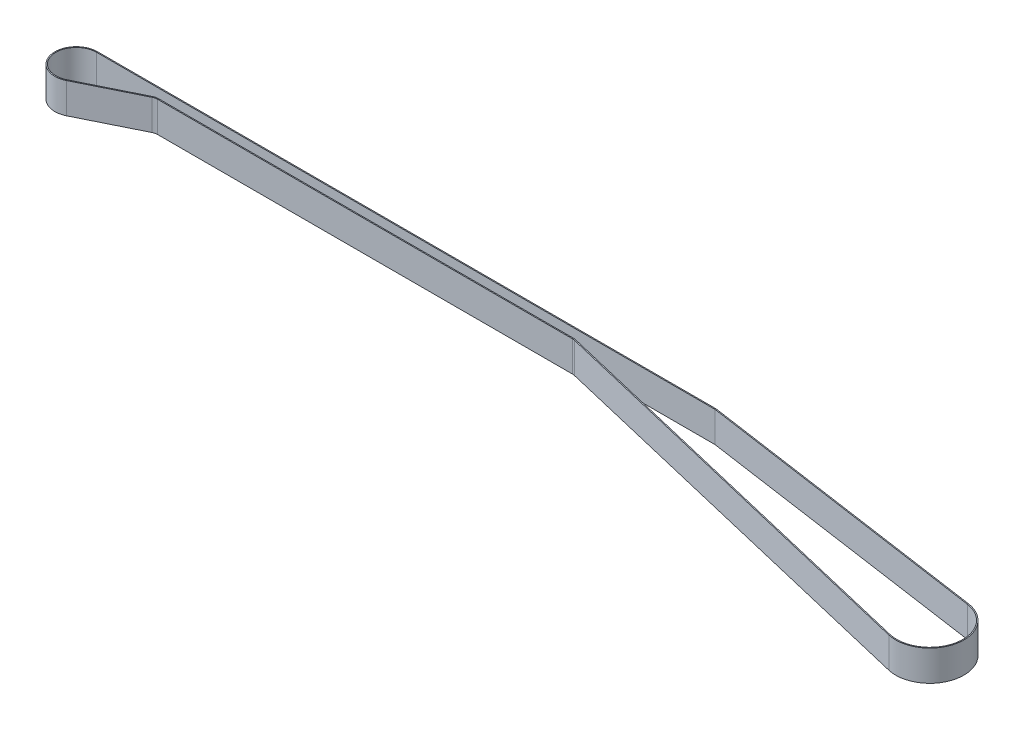
SolidWorks part; units mm, degrees
ref_plane "Front Plane" through (0, 0, 0) normal (0, 0, 1) x (1, 0, 0)
ref_plane "Top Plane" through (0, 0, 0) normal (0, 1, 0) x (1, 0, 0)
ref_plane "Right Plane" through (0, 0, 0) normal (1, 0, 0) x (0, 0, -1)
sketch "Sketch2" plane through (0, 0, 0) normal (0, 1, 0) x (1, 0, 0)
  line L0 (0, 10) -> (303.94, 10)
  line L1 (303.94, 10) -> (448.8416, -10.9167)
  line L2 (240.1117, 5.351) -> (442.7628, -42.8097)
  line L3 (4.4286, -8.9659) -> (32.5643, 4.9313)
  line L4 (35, 5.5) -> (238.84, 5.5)
  line L5 (0, 10.5) -> (303.9759, 10.5)
  line L6 (303.9759, 10.5) -> (448.9131, -10.4218)
  line L7 (239.9961, 4.8645) -> (442.6472, -43.2961)
  line L8 (35, 5) -> (238.84, 5)
  line L9 (4.65, -9.4142) -> (32.7857, 4.483)
  circle A0 centre (0, 0) radius 10 construction
  circle A1 centre (35, 0) radius 5.5 construction
  circle A2 centre (238.84, 0) radius 5.5 construction
  circle A3 centre (303.94, 0) radius 10 construction
  circle A4 centre (446.52, -27) radius 16.25 construction
  arc A5 (0, 10) -> (4.4286, -8.9659) centre (0, 0) ccw
  arc A6 (35, 5.5) -> (32.5643, 4.9313) centre (35, 0) ccw
  arc A7 (240.1117, 5.351) -> (238.84, 5.5) centre (238.84, 0) ccw
  arc A8 (442.7628, -42.8097) -> (448.8416, -10.9167) centre (446.52, -27) ccw
  arc A9 (442.6472, -43.2961) -> (448.9131, -10.4218) centre (446.52, -27) ccw
  arc A10 (239.9961, 4.8645) -> (238.84, 5) centre (238.84, 0) ccw
  arc A11 (35, 5) -> (32.7857, 4.483) centre (35, 0) ccw
  arc A12 (0, 10.5) -> (4.65, -9.4142) centre (0, 0) ccw
  dimension "D1" = 20
  dimension "D2" = 11
  dimension "D3" = 11
  dimension "D4" = 20
  dimension "D5" = 32.5
  dimension "D6" = 35
  dimension "D7" = 203.84
  dimension "D8" = 65.1
  dimension "D9" = 27
  dimension "D10" = 142.58
  dimension "D11" = 0.5
extrude "Boss-Extrude1" add sketch "Sketch2" along normal blind 15
